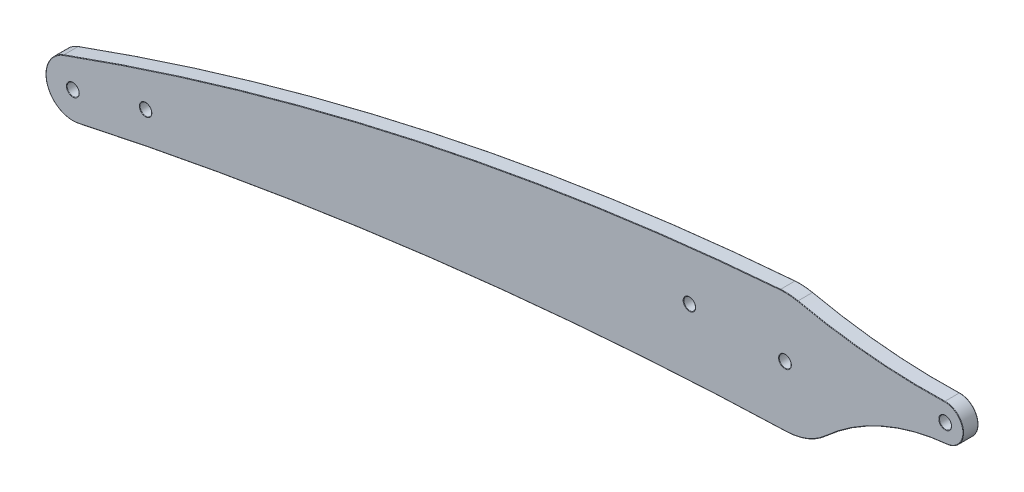
SolidWorks part; units mm, degrees
ref_plane "Front Plane" through (0, 0, 0) normal (0, 0, 1) x (1, 0, 0)
ref_plane "Top Plane" through (0, 0, 0) normal (0, 1, 0) x (1, 0, 0)
ref_plane "Right Plane" through (0, 0, 0) normal (1, 0, 0) x (0, 0, -1)
sketch "Sketch1" plane through (0, 0, 0) normal (0, 0, 1) x (1, 0, 0)
  line L0 (-273.7014, 238.8239) -> (16.1627, 287.9649) construction
  line L1 (-273.7014, 238.8239) -> (16.1627, 287.9649) construction
  circle A0 centre (-273.7014, 238.8239) radius 9 construction
  circle A1 centre (-37.0777, 278.939) radius 10 construction
  circle A2 centre (-37.0777, 278.939) radius 20 construction
  circle A3 centre (16.1627, 287.9649) radius 6 construction
  arc A4 (-276.7803, 247.2809) -> (-38.6275, 298.8789) centre (31.1135, -598.4149) cw
  arc A5 (-271.7936, 230.0285) -> (-36.4587, 258.9486) centre (3.7765, -1040.4286) cw
  arc A6 (-32.8087, 298.4781) -> (15.9797, 293.9621) centre (9.8804, 493.8691) ccw
  arc A7 (-23.6319, 264.1333) -> (16.7363, 281.9924) centre (23.4283, 212.313) cw
  arc A8 (-38.6275, 298.8789) -> (-32.8087, 298.4781) centre (-37.0777, 278.939) cw
  arc A9 (-23.6319, 264.1333) -> (-36.4587, 258.9486) centre (-37.0777, 278.939) cw
  arc A10 (15.9797, 293.9621) -> (16.7363, 281.9924) centre (16.1627, 287.9649) cw
  arc A11 (-276.7803, 247.2809) -> (-271.7936, 230.0285) centre (-273.7014, 238.8239) ccw
  arc A12 (-273.7014, 238.8239) -> (16.1627, 287.9649) centre (120.7432, -1208.3849) cw construction
  circle A13 centre (-273.7014, 238.8239) radius 2
  circle A14 centre (-249.5273, 245.1968) radius 1.95
  circle A15 centre (-68.8277, 279.5878) radius 1.95
  circle A16 centre (-37.0777, 278.939) radius 2
  circle A17 centre (16.1627, 287.9649) radius 2
  point P2 (-37.0777, 278.939)
  point P26 (-68.8277, 279.5878)
  point P27 (-249.5273, 245.1968)
  dimension "D1" = 18
  dimension "D2" = 40
  dimension "D3" = 20
  dimension "D4" = 12
  dimension "D5" = 1300
  dimension "D6" = 900
  dimension "D7" = 200
  dimension "D8" = 70
  dimension "D9" = 1500
  dimension "D12" = 4
  dimension "D13" = 3.9
  dimension "D14" = 4
  dimension "D10" = 31.75
  dimension "D11" = 25
extrude "Boss-Extrude1" add sketch "Sketch1" against normal blind 5
fillet "Fillet1" radius 0.15 26 edges at (-154.7868, 249.865, -5) (-29.5827, 260.3965, -5) (-4.8924, 276.3281, -5) (22.1507, 288.3434, -5) (-8.5533, 294.7204, -5) (-35.7034, 298.8918, -5) (-159.4582, 281.1773, -5) (-282.3474, 236.3248, -5) (-271.7014, 238.8239, -5) (-247.5773, 245.1968, -5) (-66.8777, 279.5878, -5) (-35.0777, 278.939, -5) (18.1627, 287.9649, -5) (-159.4582, 281.1773, 0) (-35.7034, 298.8918, 0) (-8.5533, 294.7204, 0) (22.1507, 288.3434, 0) (-4.8924, 276.3281, 0) (-29.5827, 260.3965, 0) (-154.7868, 249.865, 0) (-282.3474, 236.3248, 0) (-271.7014, 238.8239, 0) (-247.5773, 245.1968, 0) (-66.8777, 279.5878, 0) (-35.0777, 278.939, 0) (18.1627, 287.9649, 0)
